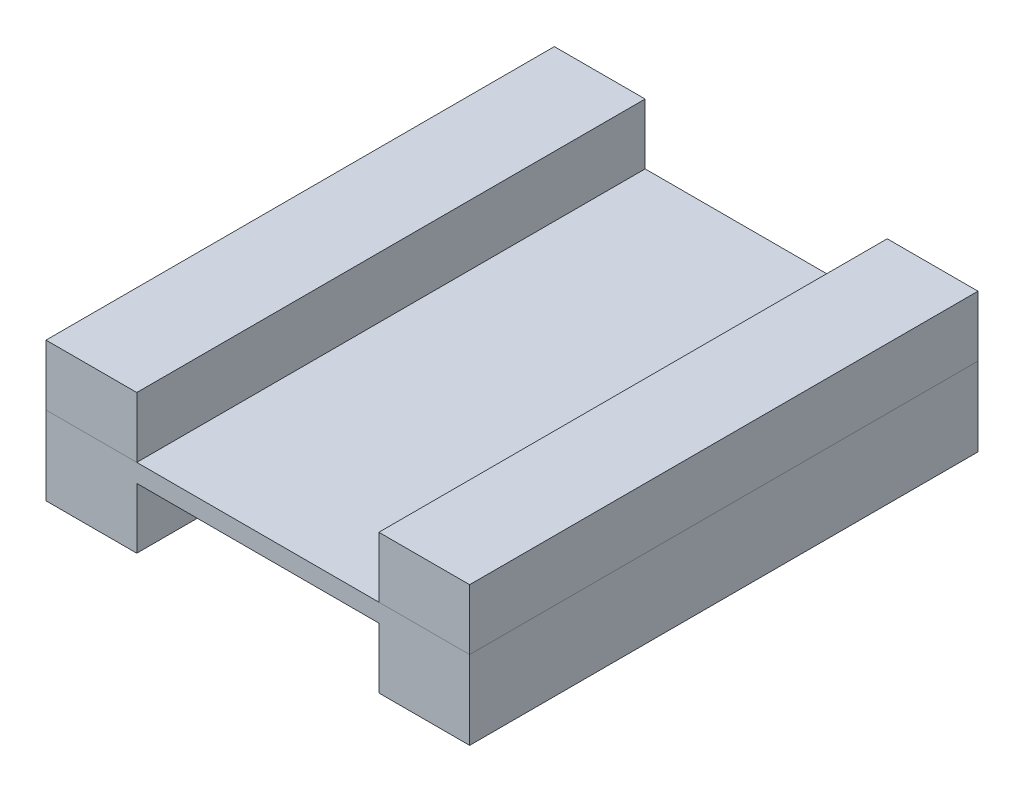
SolidWorks part; units mm, degrees
ref_plane "Front Plane" through (0, 0, 0) normal (0, 0, 1) x (1, 0, 0)
ref_plane "Top Plane" through (0, 0, 0) normal (0, 1, 0) x (1, 0, 0)
ref_plane "Right Plane" through (0, 0, 0) normal (1, 0, 0) x (0, 0, -1)
sketch "Sketch1" plane through (0, 0, 0) normal (0, 1, 0) x (1, 0, 0)
  line L1 (35, -42) -> (-35, -42)
  line L2 (35, -42) -> (35, 42)
  line L3 (35, 42) -> (-35, 42)
  line L4 (-35, -42) -> (-35, 42)
  line L5 (35, -42) -> (-35, 42) construction
  line L6 (35, 42) -> (-35, -42) construction
  point P0 (0, 0)
  dimension "D1" = 70
  dimension "D2" = 84
extrude "Boss-Extrude1" add sketch "Sketch1" along normal blind 3
sketch "Sketch2" plane through (0, 3, 0) normal (0, 1, 0) x (1, 0, 0)
  line L1 (-35, 42) -> (-20, 42)
  line L2 (-35, 42) -> (-35, -42)
  line L3 (-35, -42) -> (-20, -42)
  line L4 (-20, 42) -> (-20, -42)
  line L5 (35, 42) -> (20, 42)
  line L6 (35, 42) -> (35, -42)
  line L7 (35, -42) -> (20, -42)
  line L8 (20, 42) -> (20, -42)
  dimension "D1" = 15
  dimension "D2" = 15
  dimension "D3" = 84
  dimension "D4" = 84
extrude "Boss-Extrude2" add sketch "Sketch2" along normal blind 10 separate body
ref_plane "Plane1" through (0, 1.5, 0) normal (0, -1, 0) x (-1, 0, 0)
mirror "Mirror3" about plane through (0, 1.5, 0) normal (0, -1, 0) of "Boss-Extrude2"
